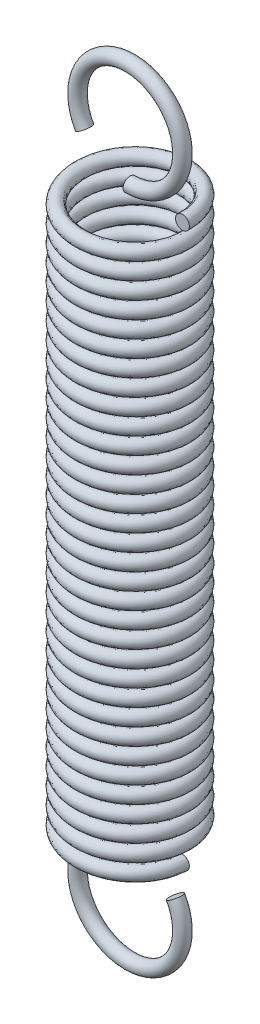
SolidWorks part; units mm, degrees
material "AISI 304"
ref_plane "Front Plane" through (0, 0, 0) normal (0, 0, 1) x (1, 0, 0)
ref_plane "Top Plane" through (0, 0, 0) normal (0, 1, 0) x (1, 0, 0)
ref_plane "Right Plane" through (0, 0, 0) normal (1, 0, 0) x (0, 0, -1)
sketch "Sketch1" plane through (0, 0, 0) normal (0, 0, 1) x (1, 0, 0)
  line L0 (0, 0) -> (14.826, 0) construction
  line L1 (0, 0) -> (0, -3) construction
  line L2 (-3, 0) -> (-3, -3) construction
  line L3 (-3, 0) -> (3, 0)
  line L4 (-3, 0) -> (-3, 28)
  line L5 (-3, 28) -> (3, 28)
  line L6 (3, 0) -> (3, 28)
  line L7 (3, 0) -> (3, -3) construction
  line L8 (0, 31) -> (0, 0) construction
  line L10 (0, 34) -> (-3, 34) construction
  line L11 (0, -6) -> (-3, -6) construction
  line L12 (0, 29) -> (-3.8337, 29) construction
  line L13 (-3, 23) -> (3, 23) construction
  circle A0 centre (0, -3) radius 3
  circle A1 centre (0, 31) radius 3
  circle A2 centre (0, 26) radius 3 construction
  circle A3 centre (2.65, 0) radius 0.35
  circle A4 centre (0, 31) radius 2.3
  circle A5 centre (0, -3) radius 2.3
  circle A6 centre (0, -0.35) radius 0.35
  dimension "D1" = 6
  dimension "D4" = 0.7
  dimension "D2" = 40
  dimension "D3" = 35
sketch "Sketch2" plane through (0, 0, 0) normal (0, 1, 0) x (1, 0, 0)
  circle A0 centre (0, 0) radius 2.65
curve "Helix/Spiral1" pitch 0.8485 height 28 turns 33
sketch "Sketch3" plane through (0, 0, 0) normal (0, 0, 1) x (1, 0, 0)
  circle A0 centre (2.65, 0) radius 0.35 construction
  circle A1 centre (2.65, 0) radius 0.35
sweep "Sweep1" add profiles "Sketch3" path "Helix/Spiral1"
sketch "Sketch4" plane through (0, 0, 0) normal (1, 0, 0) x (0, 0, -1)
  line L0 (0, 31) -> (0, 0) construction
  line L1 (0, -0.35) -> (0, 29) construction
  line L2 (0, -3) -> (-3.9017, -3) construction
  line L3 (0, 31) -> (-2.4397, 31) construction
  line L6 (0, 28.7) -> (-0.8196, 28.7) construction
  circle A0 centre (0, 28.35) radius 0.35 construction
  circle A1 centre (0, -0.35) radius 0.35
revolve "Revolve1" add sketch "Sketch4" angle 300 about L2
sketch "Sketch7" plane through (0, 0, 0) normal (1, 0, 0) x (0, 0, -1)
  line L0 (0, 31) -> (-2.4397, 31) construction
  line L1 (0, 31) -> (-2.4397, 31) construction
  circle A0 centre (0, 28.35) radius 0.35 construction
  circle A1 centre (0, 28.35) radius 0.35
revolve "Revolve2" add sketch "Sketch7" angle 300 about L1
